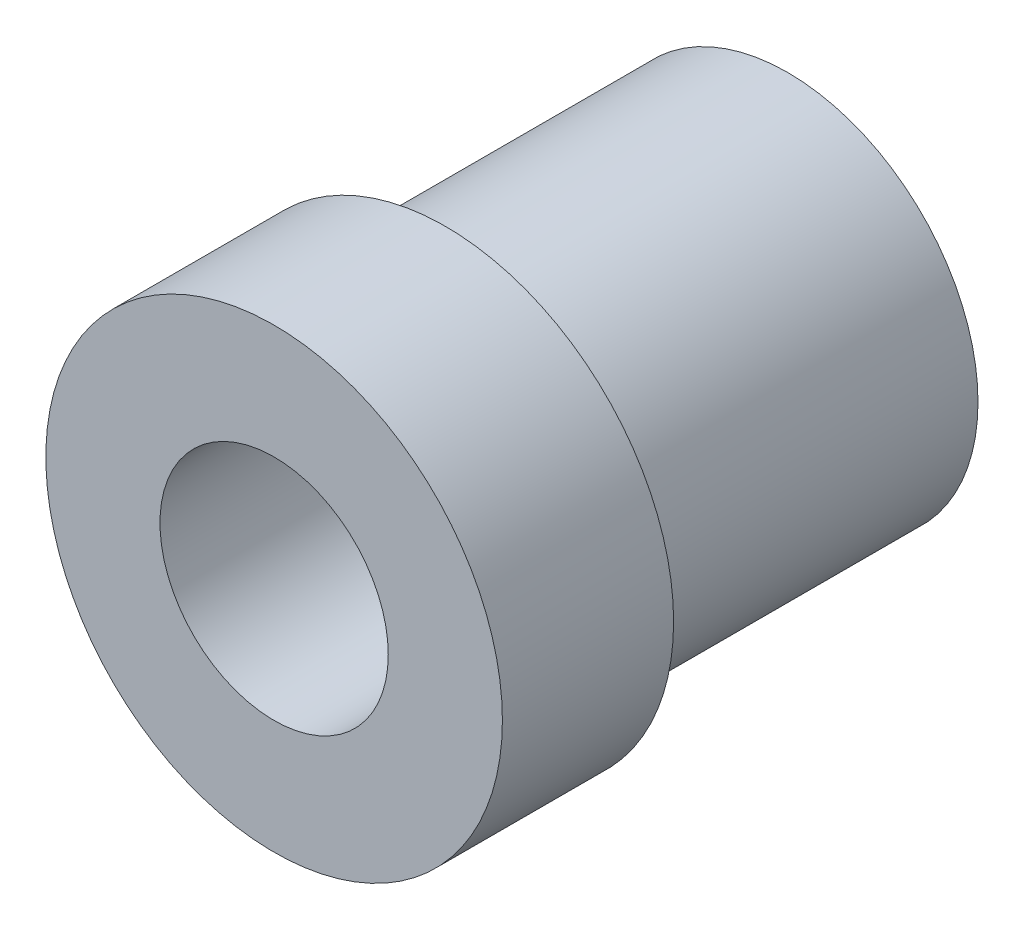
SolidWorks part; units mm, degrees
ref_plane "Front Plane" through (0, 0, 0) normal (0, 0, 1) x (1, 0, 0)
ref_plane "Top Plane" through (0, 0, 0) normal (0, 1, 0) x (1, 0, 0)
ref_plane "Right Plane" through (0, 0, 0) normal (1, 0, 0) x (0, 0, -1)
sketch "Sketch1" plane through (0, 0, 0) normal (0, 0, 1) x (1, 0, 0)
  circle A0 centre (0, 0) radius 5
  dimension "D1" = 10
extrude "Boss-Extrude1" add sketch "Sketch1" along normal blind 9
sketch "Sketch2" plane through (0, 0, 9) normal (0, 0, 1) x (1, 0, 0)
  circle A0 centre (0, 0) radius 6
  dimension "D1" = 12
extrude "Boss-Extrude2" add sketch "Sketch2" along normal blind 4.5
sketch "Sketch4" plane through (0, 0, 13.5) normal (0, 0, 1) x (1, 0, 0)
  circle A0 centre (0, 0) radius 3
  dimension "D1" = 6
extrude "Cut-Extrude1" cut sketch "Sketch4" against normal through all
